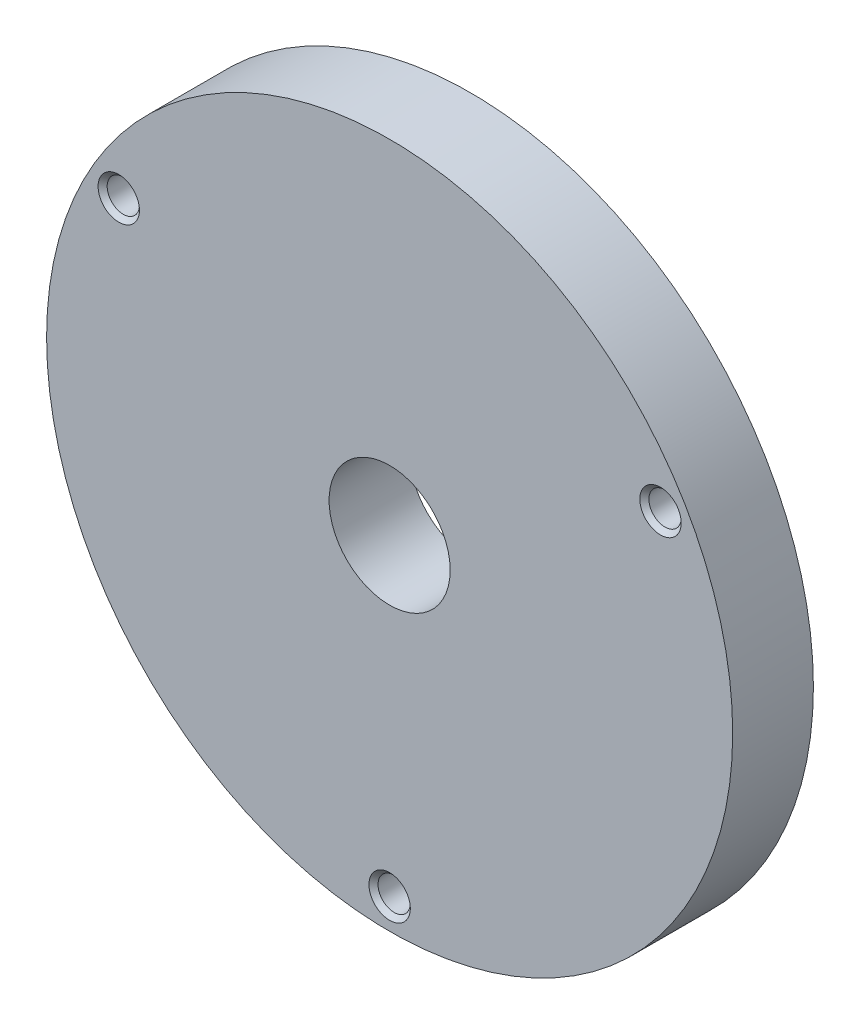
SolidWorks part; units mm, degrees
ref_plane "Front Plane" through (0, 0, 0) normal (0, 0, 1) x (1, 0, 0)
ref_plane "Top Plane" through (0, 0, 0) normal (0, 1, 0) x (1, 0, 0)
ref_plane "Right Plane" through (0, 0, 0) normal (1, 0, 0) x (0, 0, -1)
sketch "Sketch1" plane through (0, 0, 0) normal (0, 0, 1) x (1, 0, 0)
  circle A0 centre (0, 0) radius 17
  dimension "D1" = 34
extrude "Boss-Extrude1" add sketch "Sketch1" against normal blind 4
hole_wizard "M2x0.4 Tapped Hole1" positions "Sketch2" profile "Sketch3" tap size "M2x0.4" standard "ANSI Metric" end condition through all
sketch "Sketch2" plane through (0, 0, 0) normal (0, 0, 1) x (1, 0, 0)
  line L0 (0, 0) -> (0, -15.5) construction
  point P0 (0, -15.5)
  dimension "D1" = 15.5
sketch "Sketch3" plane through (0, -15.5, 0) normal (1, 0, 0) x (0, -1, 0)
  line L0 (0, 0) -> (0, 4)
  line L1 (0, 4) -> (0.8, 4)
  line L2 (0.8, 4) -> (0.8, 0.225)
  line L3 (0.8, 0.225) -> (1.025, 0)
  line L5 (1.025, 0) -> (0, 0)
  line L6 (-0.8, 0.225) -> (-1.025, 0) construction
  line L11 (0, -6.35) -> (0, 107.95) construction
  dimension "Thread Major Dia." = 1.6
  dimension "Thru Tap Drill Depth" = 4
  dimension "Near C'Sink Dia." = 2.05
  dimension "Near C'Sink Angle" = 90
pattern_circular "CirPattern1" count 3 over 360 about axis through (0, 0, 0) along (0, 0, 1) of "M2x0.4 Tapped Hole1"
sketch "Sketch4" plane through (0, 0, 0) normal (0, 0, 1) x (1, 0, 0)
  circle A0 centre (0, 0) radius 3
  dimension "D1" = 6
extrude "Cut-Extrude1" cut sketch "Sketch4" against normal through all
